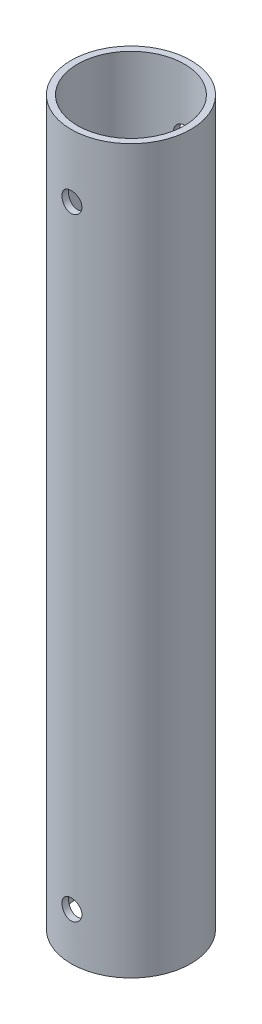
SolidWorks part; units mm, degrees
material "6061-O (SS)"
ref_plane "Alzado" through (0, 0, 0) normal (0, 0, 1) x (1, 0, 0)
ref_plane "Planta" through (0, 0, 0) normal (0, 1, 0) x (1, 0, 0)
ref_plane "Vista lateral" through (0, 0, 0) normal (1, 0, 0) x (0, 0, -1)
sketch "Croquis2" plane through (0, 0, 0) normal (0, 1, 0) x (1, 0, 0)
  circle A0 centre (0, 0) radius 9.525
  circle A1 centre (0, 0) radius 8.5
  dimension "D1" = 19.05
  dimension "D2" = 17
extrude "Saliente-Extruir1" add sketch "Croquis2" along normal blind 115
sketch "Croquis3" plane through (0, 0, 0) normal (0, 0, 1) x (1, 0, 0)
  line L1 (0, 115) -> (0, 0) construction
  line L2 (9.525, 115) -> (-9.525, 115) construction
  line L3 (8.5, 115) -> (-8.5, 115) construction
  line L4 (-9.525, 0) -> (9.525, 0) construction
  circle A1 centre (0, 105) radius 1.5875
  circle A2 centre (0, 7.5) radius 1.5875
  dimension "D1" = 3.175
  dimension "D2" = 10
  dimension "D3" = 7.5
extrude "Cortar-Extruir1" cut sketch "Croquis3" against normal through all both and the other way through all
